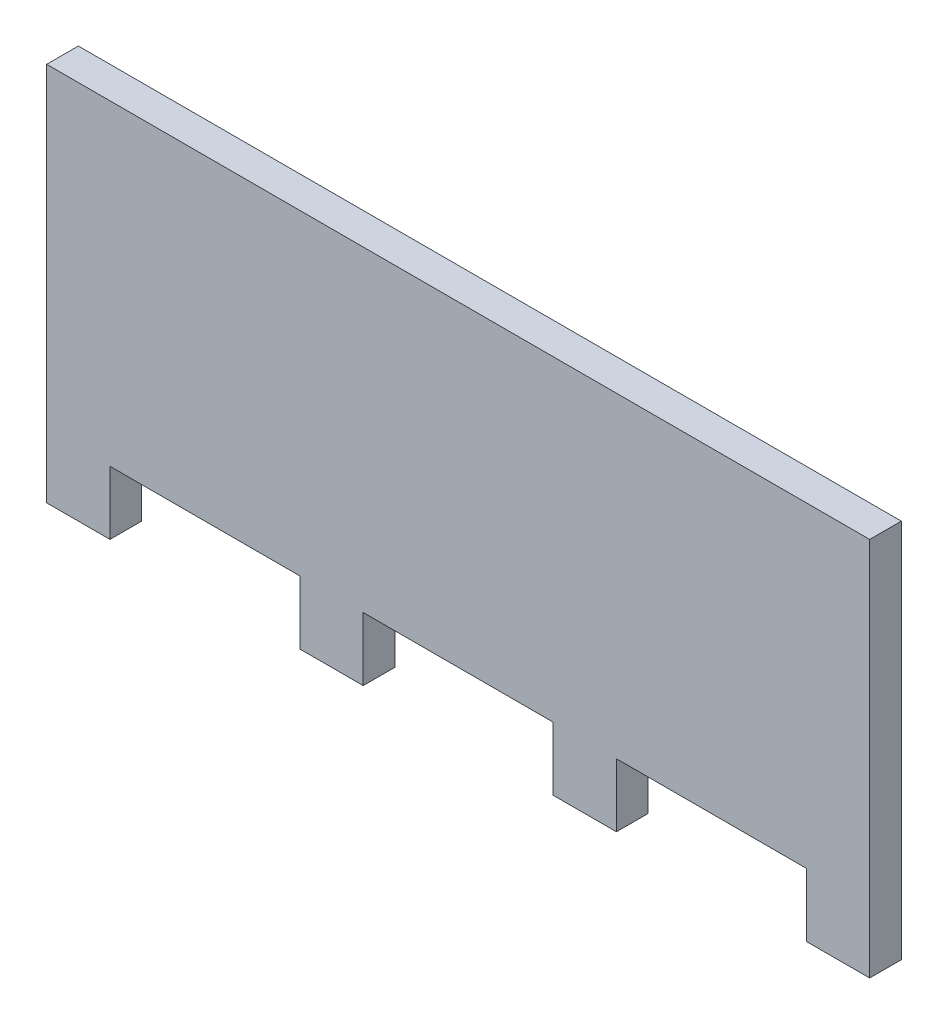
SolidWorks part; units mm, degrees
material "Balsa"
ref_plane "Plan de face" through (0, 0, 0) normal (0, 0, 1) x (1, 0, 0)
ref_plane "Plan de dessus" through (0, 0, 0) normal (0, 1, 0) x (1, 0, 0)
ref_plane "Plan de droite" through (0, 0, 0) normal (1, 0, 0) x (0, 0, -1)
sketch "Esquisse1" plane through (0, 0, 0) normal (0, 0, 1) x (1, 0, 0)
  line L1 (-65, 12.5) -> (65, 12.5)
  line L2 (-65, 12.5) -> (-65, -37.5)
  line L3 (-65, -37.5) -> (65, -37.5)
  line L4 (65, 12.5) -> (65, -37.5)
  dimension "D1" = 130
  dimension "D2" = 50
  dimension "D3" = 65
  dimension "D4" = 12.5
extrude "Boss.-Extru.1" add sketch "Esquisse1" along normal blind 5
sketch "Esquisse2" plane through (0, 0, 5) normal (0, 0, 1) x (1, 0, 0)
  line L1 (-65, -37.5) -> (-55, -37.5)
  line L2 (-65, -37.5) -> (-65, -47.5)
  line L3 (-65, -47.5) -> (-55, -47.5)
  line L4 (-55, -37.5) -> (-55, -47.5)
  dimension "D1" = 10
  dimension "D2" = 10
extrude "Boss.-Extru.2" add sketch "Esquisse2" against normal blind 5
pattern_linear "Répétition linéaire1" count 4 spacing 40 along (1, 0, 0) of "Boss.-Extru.2"
